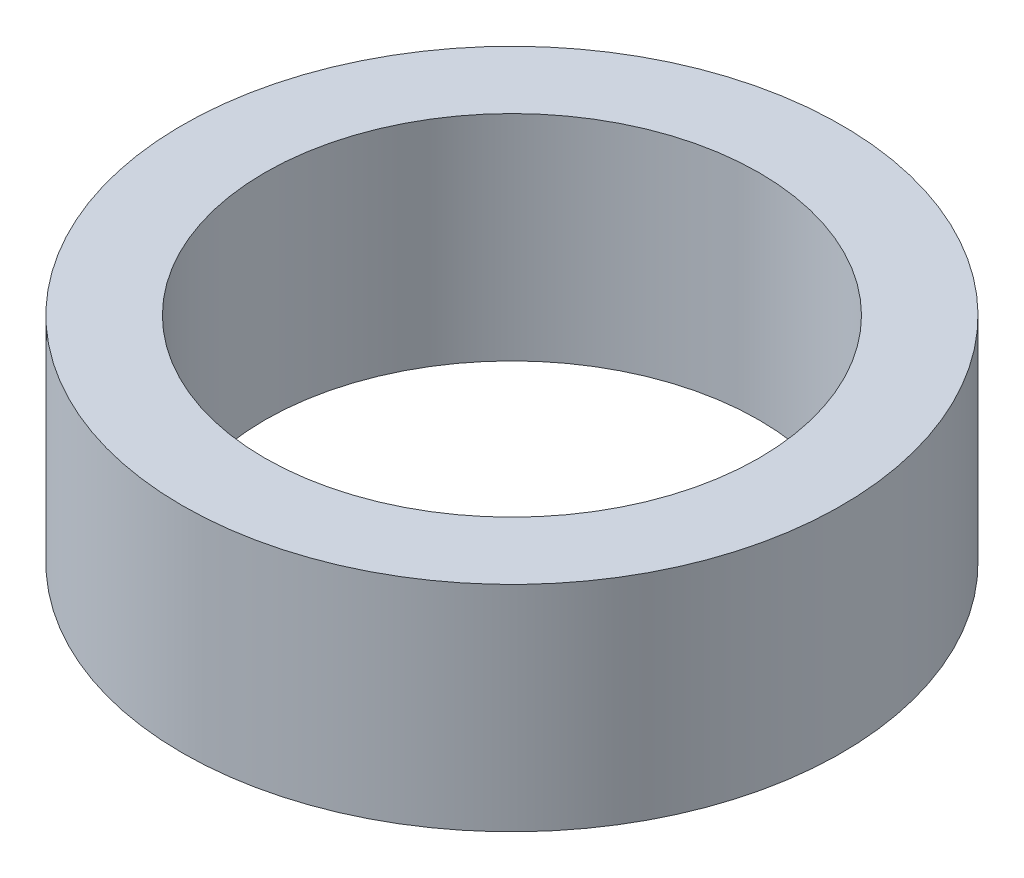
SolidWorks part; units mm, degrees
ref_plane "Front" through (0, 0, 0) normal (0, 0, 1) x (1, 0, 0)
ref_plane "Top" through (0, 0, 0) normal (0, 1, 0) x (1, 0, 0)
ref_plane "Right" through (0, 0, 0) normal (1, 0, 0) x (0, 0, -1)
sketch "Sketch1" plane through (0, 0, 0) normal (0, 1, 0) x (1, 0, 0)
  circle A0 centre (0, 0) radius 9.525
  circle A1 centre (0, 0) radius 12.7
  dimension "D1" = 19.05
  dimension "D2" = 25.4
extrude "Boss-Extrude1" add sketch "Sketch1" along normal blind 8.255
